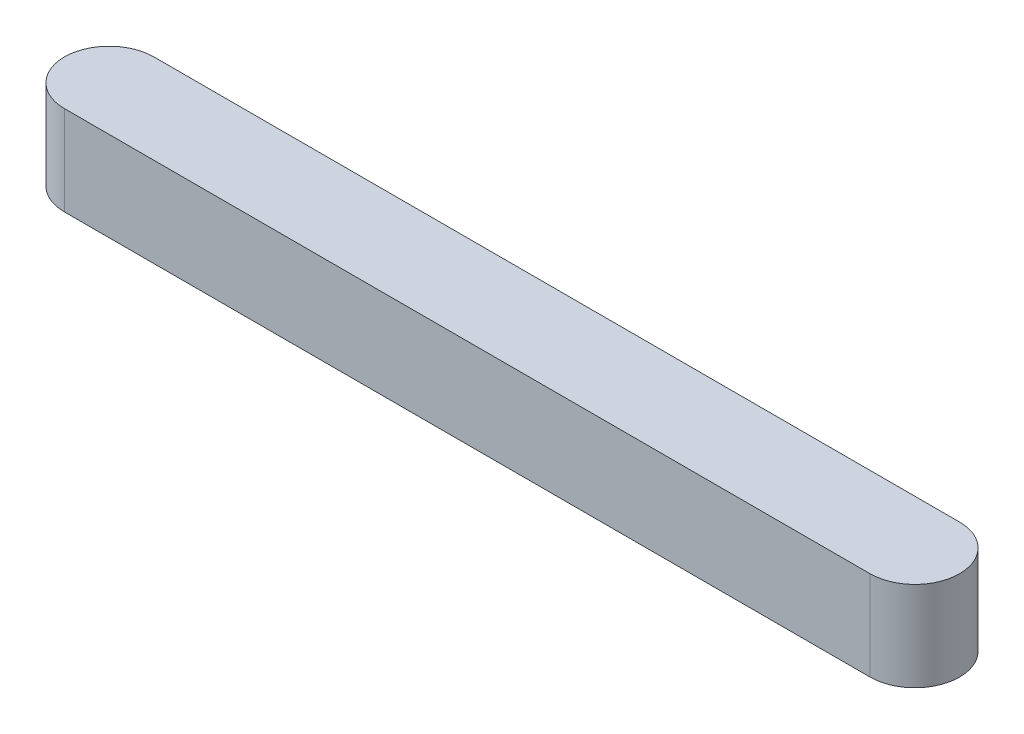
SolidWorks part; units mm, degrees
material "6061-T6 (SS)"
ref_plane "Front Plane" through (0, 0, 0) normal (0, 0, 1) x (1, 0, 0)
ref_plane "Top Plane" through (0, 0, 0) normal (0, 1, 0) x (1, 0, 0)
ref_plane "Right Plane" through (0, 0, 0) normal (1, 0, 0) x (0, 0, -1)
sketch "Sketch1" plane through (0, 0, 0) normal (0, 1, 0) x (1, 0, 0)
  line L1 (-9, 1) -> (9, 1)
  line L3 (-9, -1) -> (9, -1)
  line L5 (-9, 1) -> (9, -1) construction
  line L6 (-9, -1) -> (9, 1) construction
  arc A0 (-9, 1) -> (-9, -1) centre (-9, 0) ccw
  arc A1 (9, -1) -> (9, 1) centre (9, 0) ccw
  point P0 (0, 0)
  point P7 (8.4525, -1.0382)
  dimension "D1" = 2
  dimension "D2" = 20
extrude "Boss-Extrude1" add sketch "Sketch1" along normal blind 2
